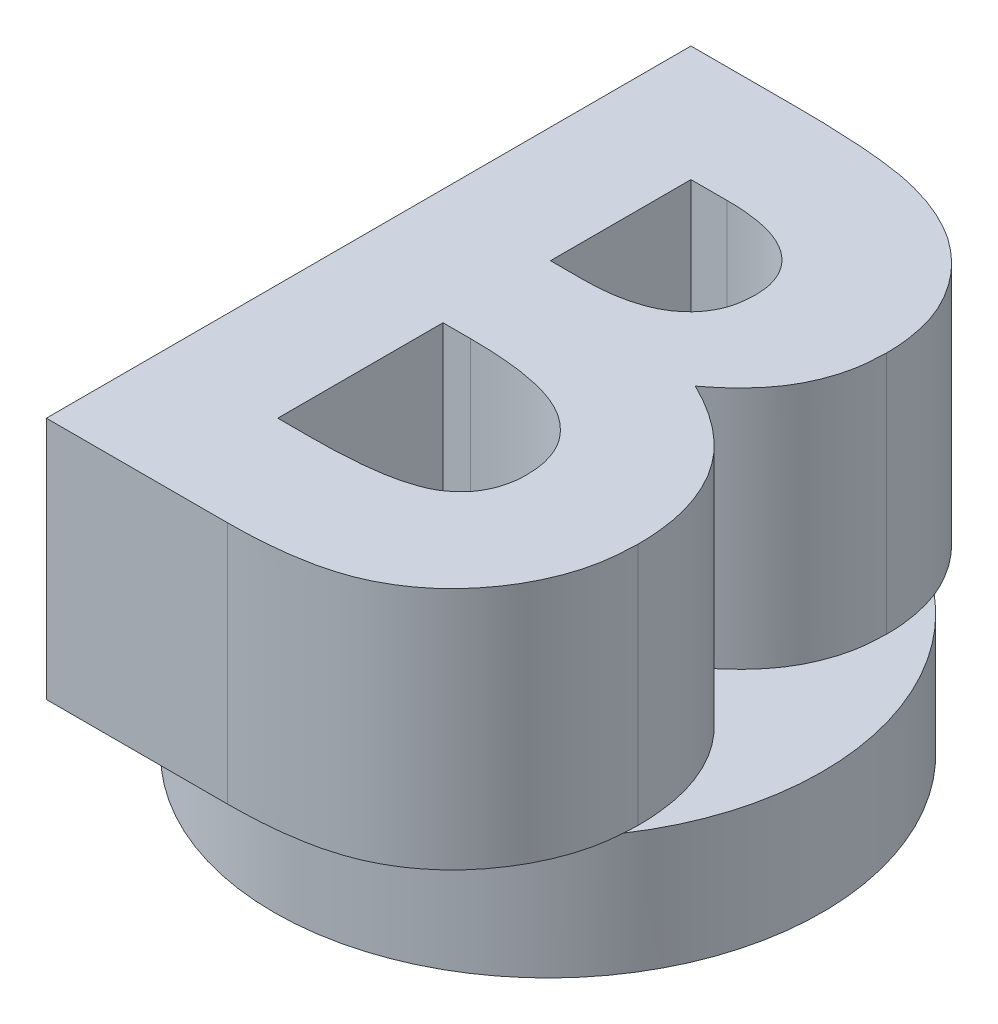
SolidWorks part; units mm, degrees
ref_plane "Front Plane" through (0, 0, 0) normal (0, 0, 1) x (1, 0, 0)
ref_plane "Top Plane" through (0, 0, 0) normal (0, 1, 0) x (1, 0, 0)
ref_plane "Right Plane" through (0, 0, 0) normal (1, 0, 0) x (0, 0, -1)
sketch "Sketch1" plane through (0, 0, 0) normal (0, 1, 0) x (1, 0, 0)
  circle A0 centre (0, 0) radius 22.5
  dimension "D1" = 45
extrude "Boss-Extrude1" add sketch "Sketch1" along normal blind 10
sketch "Sketch2" plane through (0, 10, 0) normal (0, 1, 0) x (1, 0, 0)
  text T0 "<b>B</b>" font "Century Gothic" height in points 200
extrude "Boss-Extrude2" add sketch "Sketch2" along normal blind 20
sketch "Sketch3" plane through (0, 0, 0) normal (0, -1, 0) x (1, 0, 0)
  line L0 (14.5514, 2.7786) -> (0, 30)
  line L1 (0, 30) -> (-14.5514, 2.7786)
  circle A0 centre (0, -5) radius 16.5
  circle A2 centre (0, 0) radius 22.5 construction
  circle A4 centre (0, 0) radius 21.5
  circle A5 centre (0, 0) radius 21.5
  dimension "D1" = 33
  dimension "D2" = 35
  dimension "D3" = 5
  dimension "D4" = 1
extrude "Cut-Extrude2" cut sketch "Sketch3" against normal blind 5 contours L0 A5 L1 A0 | A0
